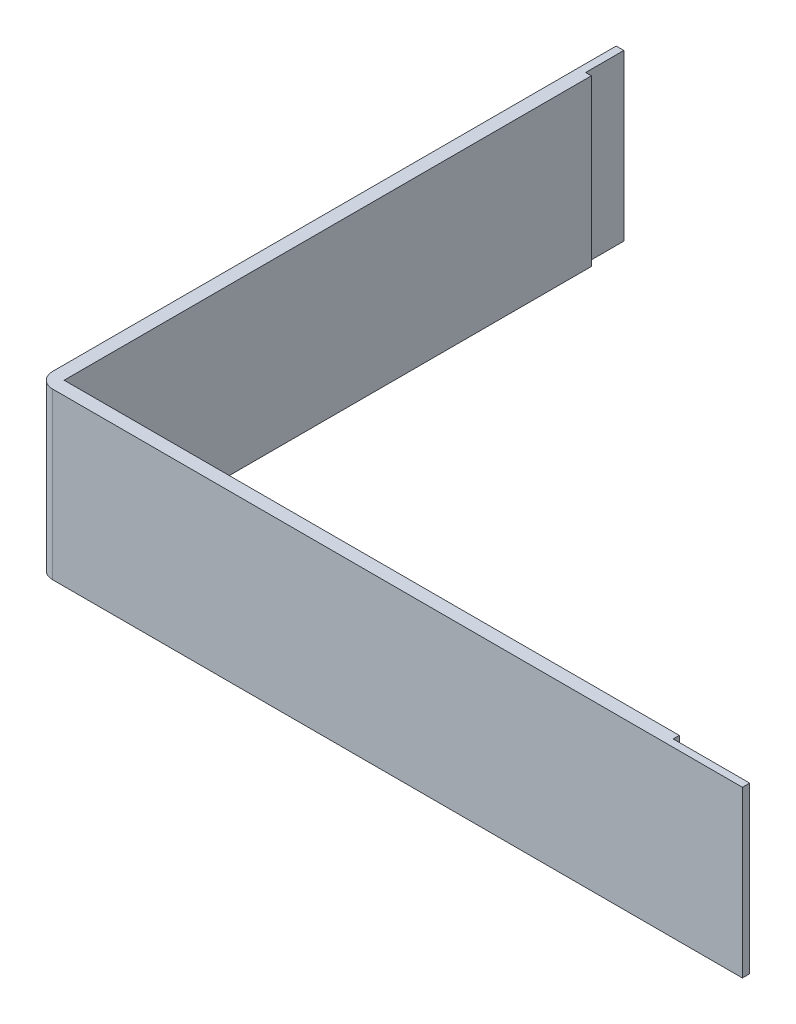
SolidWorks part; units mm, degrees
ref_plane "Alzado" through (0, 0, 0) normal (0, 0, 1) x (1, 0, 0)
ref_plane "Planta" through (0, 0, 0) normal (0, 1, 0) x (1, 0, 0)
ref_plane "Vista lateral" through (0, 0, 0) normal (1, 0, 0) x (0, 0, -1)
sketch "Croquis1" plane through (0, -0.154, 0) normal (0, 1, 0) x (1, 0, 0)
  line L0 (-59.9053, -154.5) -> (30.5947, -154.5) construction
  line L1 (-61.9053, -78.5) -> (-61.9053, -152.5) construction
  line L2 (-59.9053, -154.5) -> (30.2947, -154.5)
  line L3 (-61.9053, -78.8) -> (-61.9053, -152.5)
  line L4 (-61.9053, -78.8) -> (-60.9053, -78.8)
  line L5 (-60.9053, -78.8) -> (-60.9053, -83.8)
  line L6 (-60.9053, -83.8) -> (-60.1553, -83.8)
  line L7 (-60.1553, -83.8) -> (-60.1553, -152.75)
  line L8 (-60.1553, -152.75) -> (20.2947, -152.75)
  line L9 (20.2947, -152.75) -> (20.2947, -153.55)
  line L10 (20.2947, -153.55) -> (30.2947, -153.55)
  line L11 (30.2947, -153.55) -> (30.2947, -154.5)
  line L12 (-61.9053, -78.5) -> (-60.7053, -78.5) construction
  line L13 (-60.7053, -78.5) -> (-60.7053, -83.5) construction
  line L14 (-60.7053, -83.5) -> (-59.9053, -83.5) construction
  line L15 (-59.9053, -83.5) -> (-59.9053, -145.4384) construction
  line L16 (-59.9053, -152.5) -> (20.5947, -152.5) construction
  line L17 (20.5947, -152.5) -> (20.5947, -153.3) construction
  line L18 (30.5947, -153.3) -> (30.5947, -154.5) construction
  line L19 (20.5947, -153.3) -> (30.5947, -153.3) construction
  arc A0 (-61.9053, -152.5) -> (-59.9053, -154.5) centre (-59.9053, -152.5) ccw construction
  arc A1 (-61.9053, -152.5) -> (-59.9053, -154.5) centre (-59.9053, -152.5) ccw
  point P16 (-61.3053, -78.5)
  dimension "D1" = 0.3
  dimension "D2" = 0.2
  dimension "D3" = 0.3
  dimension "D4" = 0.25
  dimension "D5" = 0.25
  dimension "D6" = 0.3
  dimension "D7" = 0.3
  dimension "D8" = 0.25
extrude "Saliente-Extruir1" add sketch "Croquis1" along normal offset from surface (21.6 mm away) 0.2 from offset 0.2
